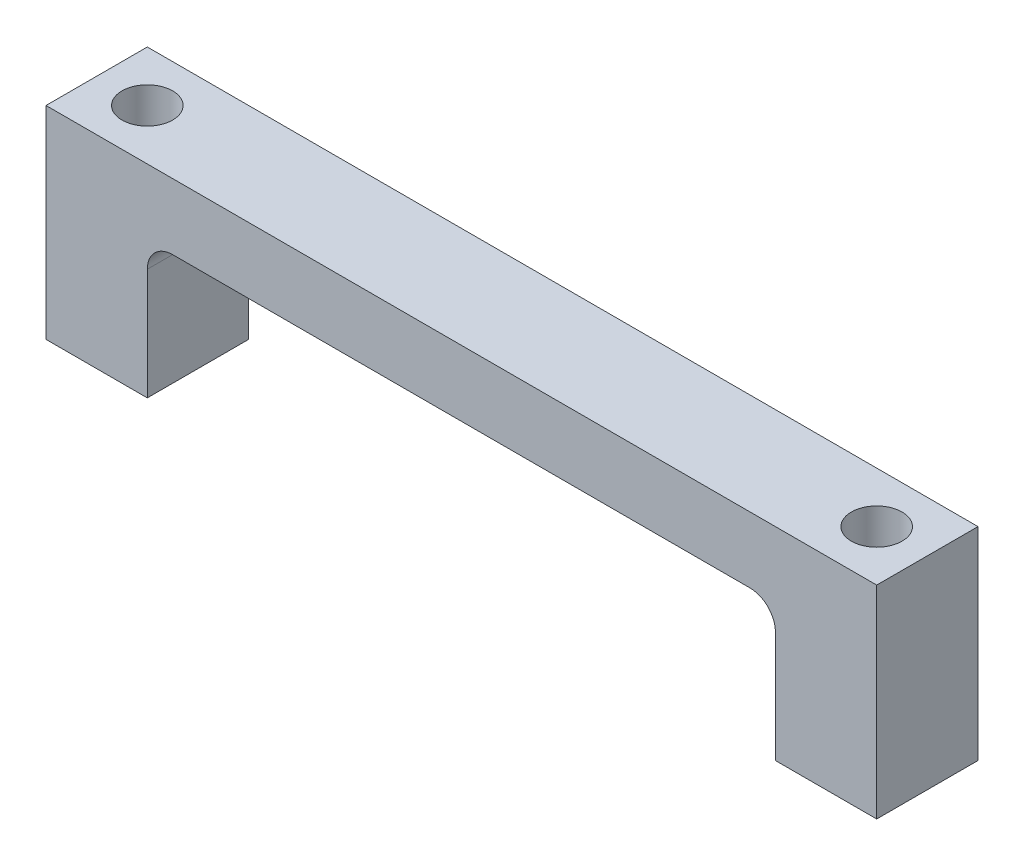
SolidWorks part; units mm, degrees
ref_plane "Front Plane" through (0, 0, 0) normal (0, 0, 1) x (1, 0, 0)
ref_plane "Top Plane" through (0, 0, 0) normal (0, 1, 0) x (1, 0, 0)
ref_plane "Right Plane" through (0, 0, 0) normal (1, 0, 0) x (0, 0, -1)
sketch "Sketch1" plane through (0, 0, 0) normal (0, 0, 1) x (1, 0, 0)
  line L0 (0, 0) -> (0, -50000) construction
  line L1 (0, 0) -> (-50000, 0) construction
  line L2 (0, 0) -> (0, 6.5)
  line L3 (41, 6.5) -> (-41, 6.5)
  line L4 (-41, 6.5) -> (-41, -13.5)
  line L5 (-41, -13.5) -> (-31, -13.5)
  line L6 (-31, -13.5) -> (-31, 0)
  line L8 (41, -13.5) -> (31, -13.5)
  line L9 (31, -13.5) -> (31, 0)
  line L10 (41, 6.5) -> (41, -13.5)
  line L11 (-31, 0) -> (31, 0)
extrude "Boss-Extrude1" add sketch "Sketch1" along normal blind 10 contours L10 L3 L2 L11 L9 L8 | L6 L11 L2 L3 L4 L5
fillet "Fillet1" radius 2.5 2 edges at (31, 0, 5) (-31, 0, 5)
sketch "Sketch2" plane through (0, 6.5, 0) normal (0, 1, 0) x (1, 0, 0)
  line L0 (0, -10) -> (0, 0) construction
  line L2 (41, -10) -> (-41, -10) construction
  line L4 (36, -5) -> (-36, -5) construction
  circle A2 centre (-36, -5) radius 2.5
  circle A3 centre (36, -5) radius 2.5
  point P7 (0, -5)
extrude "Cut-Extrude1" cut sketch "Sketch2" against normal up to next
